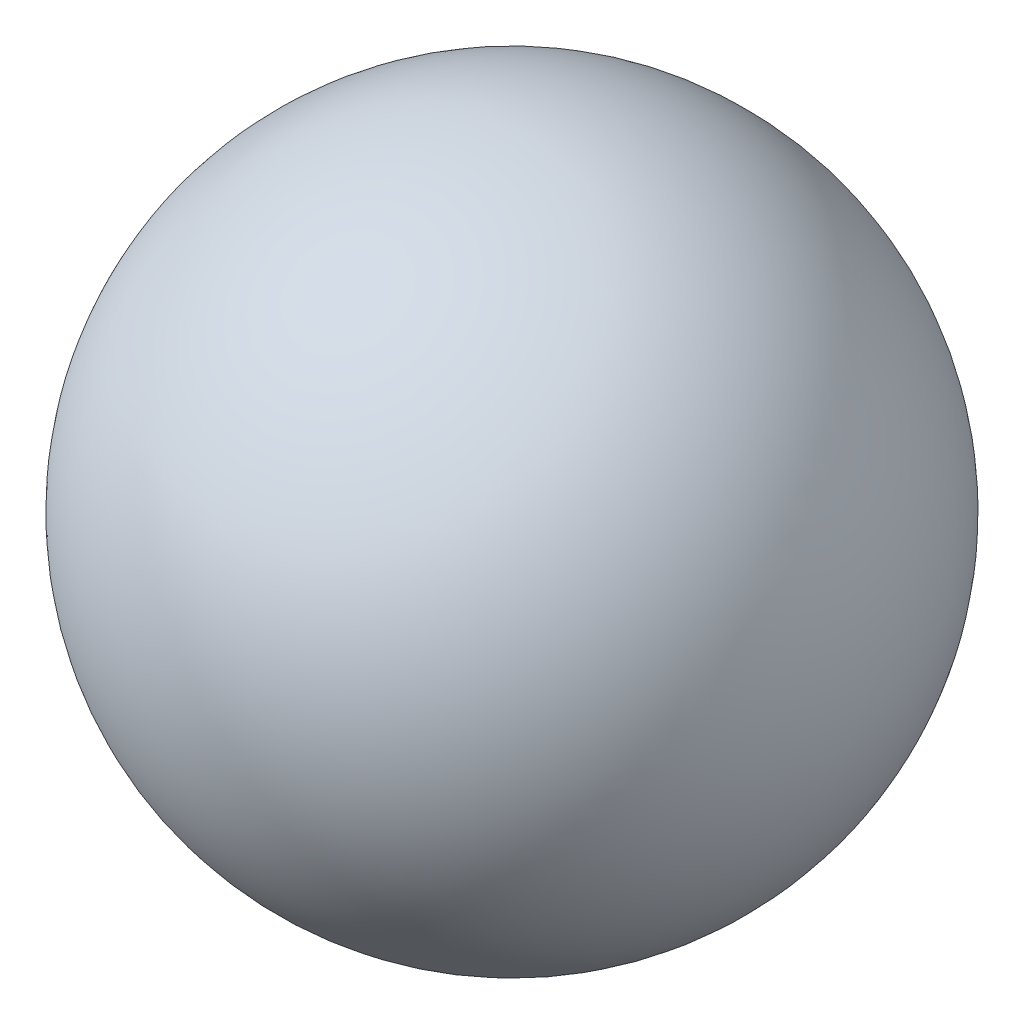
SolidWorks part; units mm, degrees
ref_plane "Front Plane" through (0, 0, 0) normal (0, 0, 1) x (1, 0, 0)
ref_plane "Top Plane" through (0, 0, 0) normal (0, 1, 0) x (1, 0, 0)
ref_plane "Right Plane" through (0, 0, 0) normal (1, 0, 0) x (0, 0, -1)
sketch "Sketch1" plane through (0, 0, 0) normal (0, 0, 1) x (1, 0, 0)
  line L0 (-30.5175, 0) -> (45.8156, 0) construction
  line L1 (-15, 0) -> (15, 0)
  arc A0 (15, 0) -> (-15, 0) centre (0, 0) ccw
  dimension "D1" = 30
revolve "Revolve3" add sketch "Sketch1" angle 360 about L0
